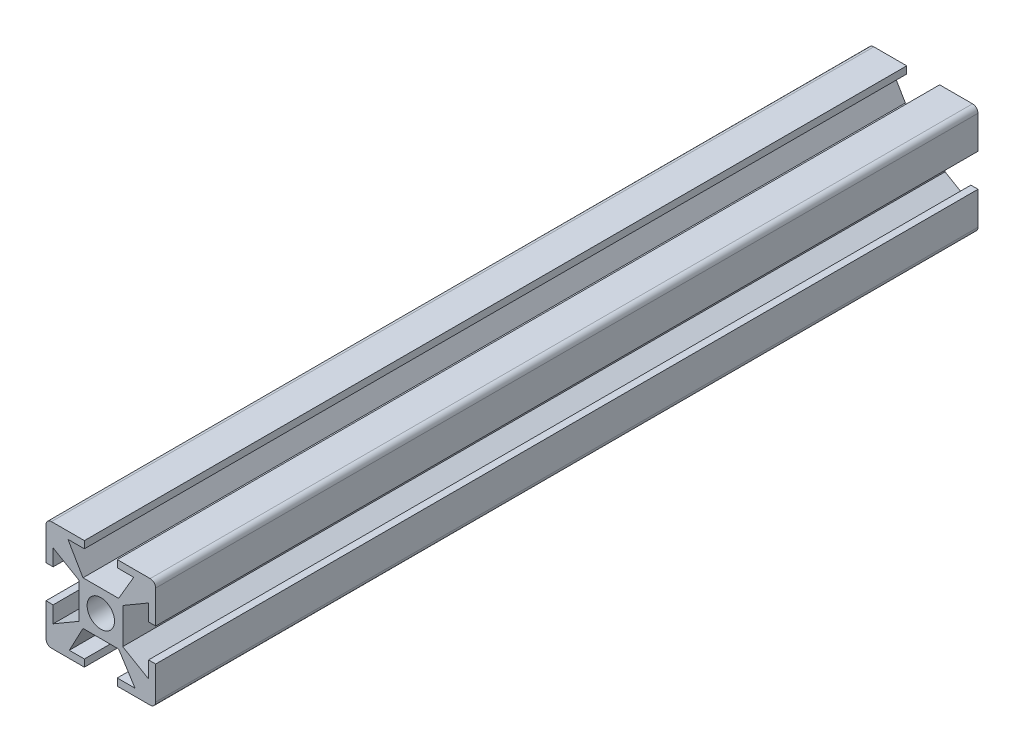
SolidWorks part; units mm, degrees
ref_plane "Alzado" through (0, 0, 0) normal (0, 0, 1) x (1, 0, 0)
ref_plane "Planta" through (0, 0, 0) normal (0, 1, 0) x (1, 0, 0)
ref_plane "Vista lateral" through (0, 0, 0) normal (1, 0, 0) x (0, 0, -1)
sketch "Croquis1" plane through (0, 0, 0) normal (0, 0, 1) x (1, 0, 0)
  line L0 (-3, 10) -> (3, 10)
  line L1 (-9, 10) -> (9, 10)
  line L2 (-10, 9) -> (-10, -9)
  line L3 (-9, -10) -> (9, -10)
  line L4 (10, 9) -> (10, -9)
  line L5 (-10, 10) -> (10, -10) construction
  line L6 (-10, -10) -> (10, 10) construction
  line L7 (-4, 4) -> (4, 4)
  line L8 (-4, 4) -> (-4, -4)
  line L9 (-4, -4) -> (4, -4)
  line L10 (4, 4) -> (4, -4)
  line L11 (-4, 4) -> (4, -4) construction
  line L12 (-4, -4) -> (4, 4) construction
  line L13 (3, 10) -> (3, 8.7)
  line L14 (-3.25, 4) -> (3.25, 4)
  line L15 (0, 10) -> (0, -10) construction
  line L16 (-10, 0) -> (10, 0) construction
  line L20 (-3, 10) -> (-3, 8.7)
  line L22 (3, -10) -> (3, -8.7)
  line L23 (-3, -10) -> (3, -10)
  line L24 (-3, -10) -> (-3, -8.7)
  line L25 (-5.75, -8.7) -> (-3, -8.7)
  line L26 (-5.75, -8.7) -> (-3.25, -4)
  line L27 (-3.25, -4) -> (3.25, -4)
  line L28 (6.25, -8.7) -> (3.25, -4)
  line L29 (3, -8.7) -> (6.25, -8.7)
  line L30 (-10, 3) -> (-10, -3)
  line L31 (-4, 3.25) -> (-4, -3.25)
  line L32 (-10, 3) -> (-8.7, 3)
  line L33 (-8.7, -6) -> (-8.7, -3)
  line L34 (-8.7, 6) -> (-4, 3.25)
  line L35 (-8.7, -6) -> (-4, -3.25)
  line L36 (-10, -3) -> (-8.7, -3)
  line L37 (-8.7, 3) -> (-8.7, 6)
  line L38 (8.7, -6) -> (4, -3.25)
  line L39 (4, 3.25) -> (4, -3.25)
  line L40 (8.7, 6) -> (4, 3.25)
  line L41 (8.7, 3) -> (8.7, 6)
  line L42 (10, 3) -> (8.7, 3)
  line L43 (10, 3) -> (10, -3)
  line L44 (10, -3) -> (8.7, -3)
  line L45 (8.7, -6) -> (8.7, -3)
  line L46 (-6, 8.7) -> (-3, 8.7)
  line L47 (-6, 8.7) -> (-3.25, 4)
  line L48 (6, 8.7) -> (3.25, 4)
  line L49 (3, 8.7) -> (6, 8.7)
  circle A0 centre (0, 0) radius 2.5
  arc A1 (-10, -9) -> (-9, -10) centre (-9, -9) ccw
  arc A2 (9, -10) -> (10, -9) centre (9, -9) ccw
  arc A3 (9, 10) -> (10, 9) centre (9, 9) cw
  arc A4 (-9, 10) -> (-10, 9) centre (-9, 9) ccw
  point P0 (0, 0)
  point P6 (0, 0)
  point P14 (0, 10)
  point P18 (0, 4)
  point P25 (0, 8.7)
  point P37 (-10, 0)
  point P40 (-4, 0)
  point P44 (-8.7, 0)
  point P56 (0, 8.7)
  dimension "D12" = 5
  dimension "D13" = 1
  dimension "D1" = 20
  dimension "D2" = 20
  dimension "D3" = 8
  dimension "D4" = 8
  dimension "D5" = 6
  dimension "D6" = 6.5
  dimension "D7" = 12
  dimension "D8" = 6.5
  dimension "D9" = 6
  dimension "D10" = 1.3
  dimension "D11" = 12
extrude "Saliente-Extruir4" add sketch "Croquis1" along normal blind 150 contours L1 A4 L2 L32 L37 L34 L8 L7 L47 L46 L20 | A3 L1 L13 L49 L48 L7 L10 L40 L41 L42 L4 | L3 A2 L4 L44 L45 L38 L10 L9 L28 L29 L22 | L2 A1 L3 L24 L25 L26 L9 L8 L35 L33 L36 | L10 L7 L8 L9 A0
